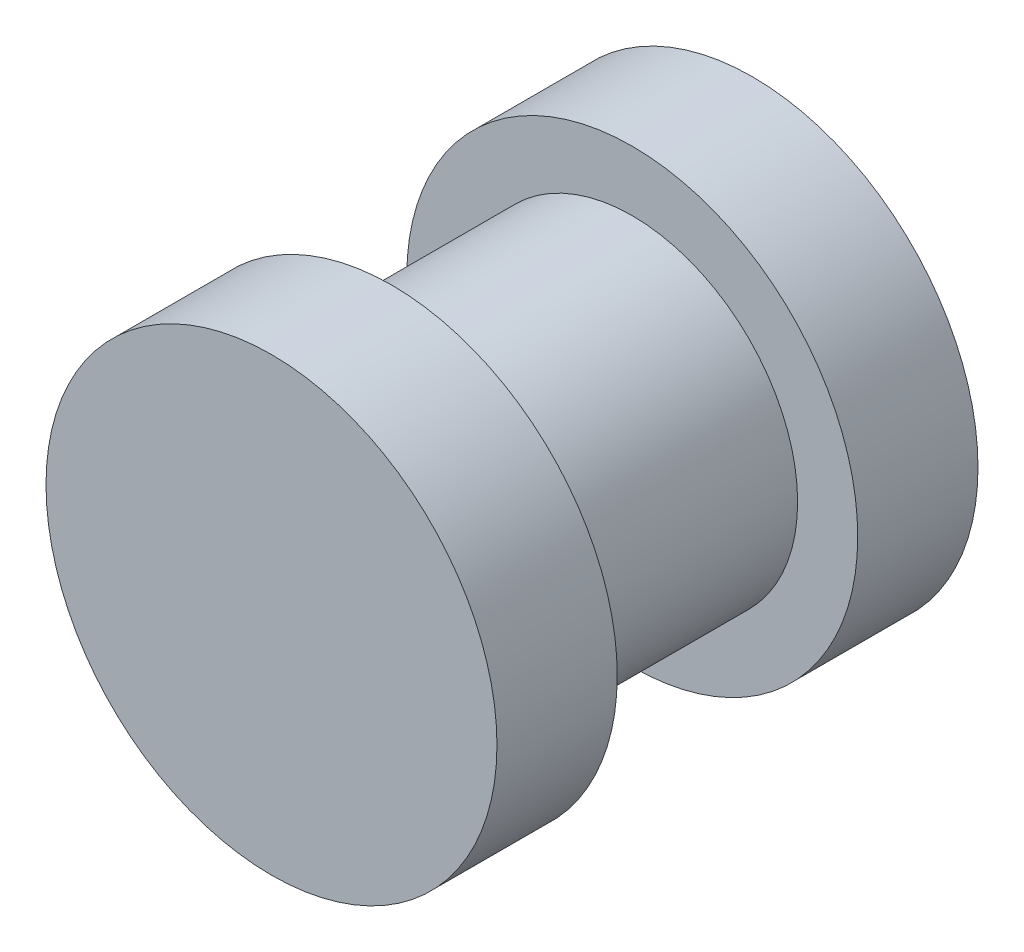
SolidWorks part; units mm, degrees
ref_plane "Front Plane" through (0, 0, 0) normal (0, 0, 1) x (1, 0, 0)
ref_plane "Top Plane" through (0, 0, 0) normal (0, 1, 0) x (1, 0, 0)
ref_plane "Right Plane" through (0, 0, 0) normal (1, 0, 0) x (0, 0, -1)
sketch "Sketch1" plane through (0, 0, 0) normal (0, 0, 1) x (1, 0, 0)
  circle A0 centre (0, 0) radius 4.7625
  dimension "D1" = 9.525
extrude "Boss-Extrude1" add sketch "Sketch1" along normal mid plane 10.16
sketch "Sketch4" plane through (0, 0, -5.08) normal (0, 0, -1) x (-1, 0, 0)
  line L1 (-1.905, -2.54) -> (1.905, -2.54)
  line L2 (-1.905, -2.54) -> (-1.905, 2.54)
  line L3 (-1.905, 2.54) -> (1.905, 2.54)
  line L4 (1.905, -2.54) -> (1.905, 2.54)
  line L5 (-1.905, -2.54) -> (1.905, 2.54) construction
  line L6 (-1.905, 2.54) -> (1.905, -2.54) construction
  point P0 (0, 0)
  dimension "D1" = 3.81
  dimension "D2" = 5.08
extrude "Cut-Extrude1" cut sketch "Sketch4" against normal blind 3.81
sketch "Sketch7" plane through (0, 0, 5.08) normal (0, 0, 1) x (1, 0, 0)
  point P0 (0, 0)
sketch "Sketch8" plane through (0, 0, 0) normal (1, 0, 0) x (0, 0, -1)
  line L0 (5.08, 4.7625) -> (-5.08, 4.7625) construction
  line L1 (-2.54, 6.0325) -> (2.54, 6.0325)
  line L2 (-2.54, 6.0325) -> (-2.54, 3.4925)
  line L3 (-2.54, 3.4925) -> (2.54, 3.4925)
  line L4 (2.54, 6.0325) -> (2.54, 3.4925)
  line L5 (-2.54, 6.0325) -> (2.54, 3.4925) construction
  line L6 (-2.54, 3.4925) -> (2.54, 6.0325) construction
  line L7 (0, 0) -> (2.128, 0) construction
  point P0 (0, 4.7625)
  dimension "D1" = 5.08
  dimension "D2" = 1.27
revolve "Cut-Revolve1" cut sketch "Sketch8" angle 360 about L7
